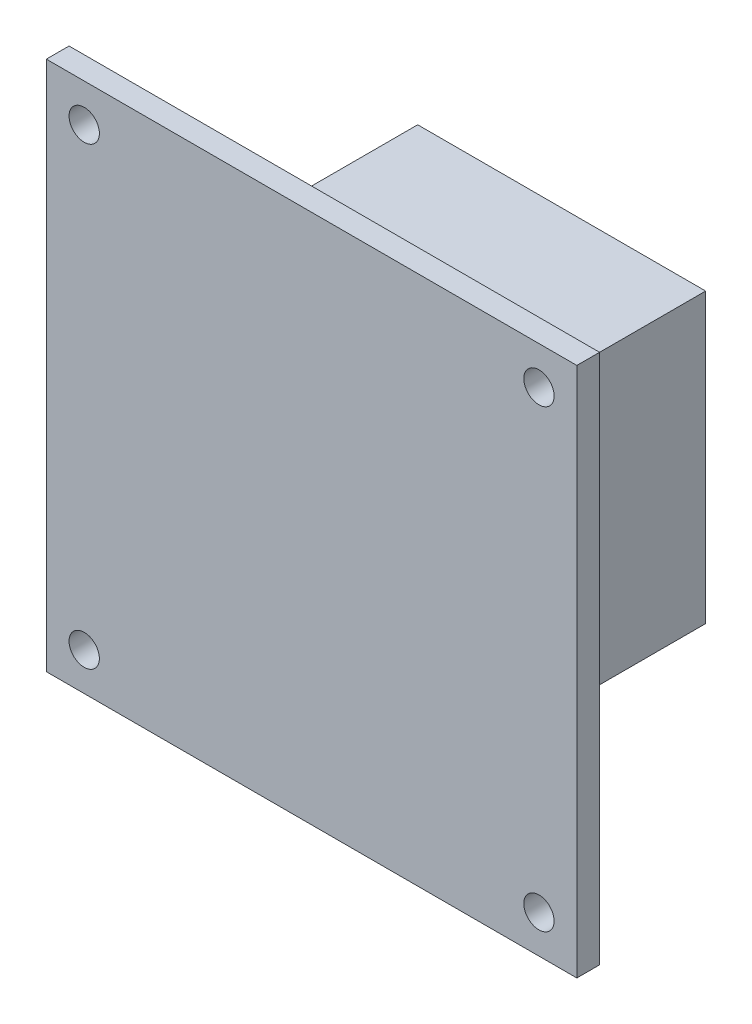
SolidWorks part; units mm, degrees
ref_plane "Front Plane" through (0, 0, 0) normal (0, 0, 1) x (1, 0, 0)
ref_plane "Top Plane" through (0, 0, 0) normal (0, 1, 0) x (1, 0, 0)
ref_plane "Right Plane" through (0, 0, 0) normal (1, 0, 0) x (0, 0, -1)
sketch "Sketch1" plane through (0, 0, 0) normal (0, 0, 1) x (1, 0, 0)
  line L1 (-35, 35) -> (35, 35)
  line L2 (-35, 35) -> (-35, -35)
  line L3 (-35, -35) -> (35, -35)
  line L4 (35, 35) -> (35, -35)
  line L5 (-35, 35) -> (35, -35) construction
  line L6 (-35, -35) -> (35, 35) construction
  point P0 (0, 0)
  dimension "D1" = 70
  dimension "D2" = 70
extrude "Boss-Extrude1" add sketch "Sketch1" along normal blind 3
sketch "Sketch3" plane through (0, 0, 3) normal (0, 0, 1) x (1, 0, 0)
  line L0 (35, 35) -> (-35, 35) construction
  line L1 (-35, 35) -> (-35, -35) construction
  circle A0 centre (-30, 30) radius 2
  circle A1 centre (30, 30) radius 2
  circle A2 centre (30, -30) radius 2
  circle A3 centre (-30, -30) radius 2
  dimension "D1" = 4
  dimension "D2" = 5
  dimension "D3" = 5
extrude "Cut-Extrude1" cut sketch "Sketch3" against normal blind 4
sketch "Sketch5" plane through (0, 0, 0) normal (0, 0, -1) x (-1, 0, 0)
  line L1 (-19, 19) -> (19, 19)
  line L2 (-19, 19) -> (-19, -19)
  line L3 (-19, -19) -> (19, -19)
  line L4 (19, 19) -> (19, -19)
  line L5 (-19, 19) -> (19, -19) construction
  line L6 (-19, -19) -> (19, 19) construction
  line L7 (-17.5, 17.5) -> (17.5, 17.5)
  line L8 (-17.5, 17.5) -> (-17.5, -17.5)
  line L9 (-17.5, -17.5) -> (17.5, -17.5)
  line L10 (17.5, 17.5) -> (17.5, -17.5)
  line L11 (-17.5, 17.5) -> (17.5, -17.5) construction
  line L12 (-17.5, -17.5) -> (17.5, 17.5) construction
  point P0 (0, 0)
  point P6 (0, 0)
  dimension "D1" = 38
  dimension "D2" = 38
  dimension "D3" = 35
  dimension "D4" = 35
extrude "Boss-Extrude2" add sketch "Sketch5" along normal blind 30
